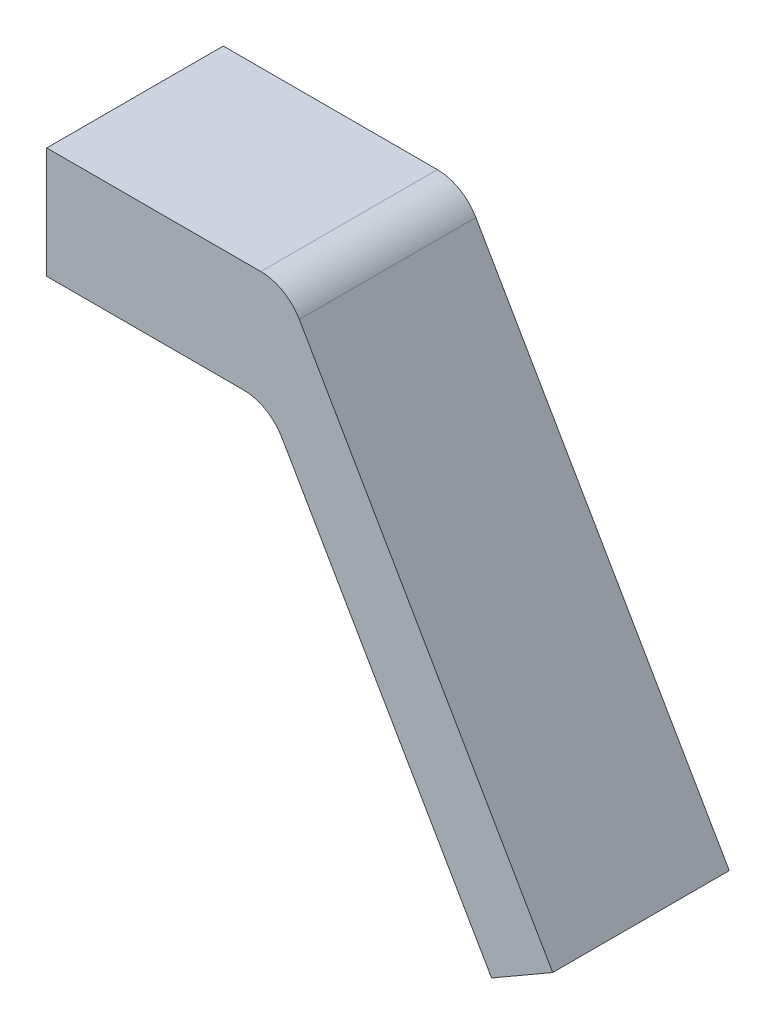
SolidWorks part; units mm, degrees
material "Stainless Steel (ferritic)"
ref_plane "Front Plane" through (0, 0, 0) normal (0, 0, 1) x (1, 0, 0)
ref_plane "Top Plane" through (0, 0, 0) normal (0, 1, 0) x (1, 0, 0)
ref_plane "Right Plane" through (0, 0, 0) normal (1, 0, 0) x (0, 0, -1)
sketch "Sketch1" plane through (0, 0, 0) normal (0, 0, 1) x (1, 0, 0)
  line L0 (-10, 0) -> (10, 0)
  line L1 (10, 0) -> (30, -34.641)
  line L2 (30, -34.641) -> (35.4993, -31.466)
  line L3 (35.4993, -31.466) -> (11.5588, 10)
  line L5 (11.5588, 10) -> (-10, 10)
  line L6 (-10, 10) -> (-10, 0)
  dimension "D1" = 10
  dimension "D2" = 6.35
  dimension "D3" = 120
  dimension "D4" = 40
  dimension "D5" = 20
extrude "Boss-Extrude1" add sketch "Sketch1" along normal blind 15.875
sketch "Sketch2" plane through (0, 0, 0) normal (0, -1, 0) x (1, 0, 0)
  line L0 (-10, 15.875) -> (10, 0) construction
  circle A0 centre (0, 7.9375) radius 5.5
  dimension "D1" = 11
extrude "Cut-Extrude1" [suppressed] cut sketch "Sketch2" against normal offset from surface (8 mm away) 2
sketch "Sketch3" [suppressed] plane through (0, 8, 0) normal (0, -1, 0) x (1, 0, 0)
  circle A0 centre (0, 7.9375) radius 4.9
  dimension "D1" = 9.8
extrude "Cut-Extrude2" [suppressed] cut sketch "Sketch3" against normal through all
fillet "Fillet1" radius 4 2 edges at (10, 0, 7.9375) (11.5588, 10, 7.9375)
